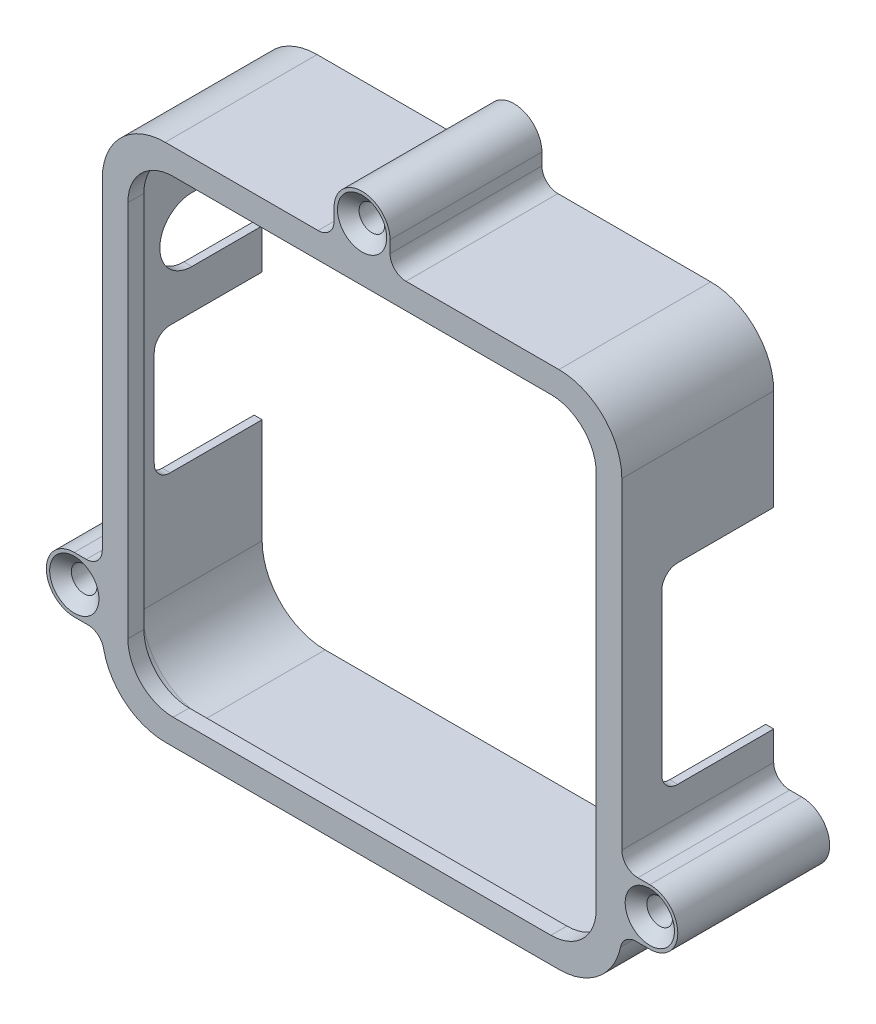
SolidWorks part; units mm, degrees
ref_plane "Front Plane" through (0, 0, 0) normal (0, 0, 1) x (1, 0, 0)
ref_plane "Top Plane" through (0, 0, 0) normal (0, 1, 0) x (1, 0, 0)
ref_plane "Right Plane" through (0, 0, 0) normal (1, 0, 0) x (0, 0, -1)
sketch "Sketch1" plane through (0, 0, 0) normal (0, 0, 1) x (1, 0, 0)
  line L1 (-50, -50) -> (50, -50)
  line L2 (-50, -50) -> (-50, 50)
  line L3 (-50, 50) -> (50, 50)
  line L4 (50, -50) -> (50, 50)
  line L5 (-50, -50) -> (50, 50) construction
  line L6 (-50, 50) -> (50, -50) construction
  line L7 (-51.5875, -51.5875) -> (51.5875, -51.5875)
  line L8 (-51.5875, -51.5875) -> (-51.5875, 51.5875)
  line L9 (-51.5875, 51.5875) -> (51.5875, 51.5875)
  line L10 (51.5875, -51.5875) -> (51.5875, 51.5875)
  line L11 (-51.5875, -51.5875) -> (51.5875, 51.5875) construction
  line L12 (-51.5875, 51.5875) -> (51.5875, -51.5875) construction
  point P0 (0, 0)
  point P6 (0, 0)
  dimension "D1" = 100
  dimension "D2" = 1.5875
extrude "Boss-Extrude1" add sketch "Sketch1" along normal blind 26.9875
fillet "Fillet1" radius 12.5 4 edges at (50, 50, 13.4937) (50, -50, 13.4937) (-50, -50, 13.4937) (-50, 50, 13.4937)
fillet "Fillet2" radius 12.5 4 edges at (51.5875, -51.5875, 13.4937) (51.5875, 51.5875, 13.4937) (-51.5875, -51.5875, 13.4937) (-51.5875, 51.5875, 13.4937)
sketch "Sketch2" plane through (0, 0, 26.9875) normal (0, 0, 1) x (1, 0, 0)
  line L0 (46.5, -37.5) -> (46.5, 37.5)
  line L1 (37.5, 46.5) -> (-37.5, 46.5)
  line L2 (-46.5, 37.5) -> (-46.5, -37.5)
  line L3 (-37.5, -46.5) -> (37.5, -46.5)
  line L4 (-39.0875, -51.5875) -> (39.0875, -51.5875)
  line L5 (51.5875, -39.0875) -> (51.5875, 39.0875)
  line L6 (39.0875, 51.5875) -> (-39.0875, 51.5875)
  line L7 (-51.5875, 39.0875) -> (-51.5875, -39.0875)
  line L8 (-39.0875, -51.5875) -> (39.0875, -51.5875)
  line L9 (51.5875, -39.0875) -> (51.5875, 39.0875)
  line L10 (39.0875, 51.5875) -> (-39.0875, 51.5875)
  line L11 (-51.5875, 39.0875) -> (-51.5875, -39.0875)
  line L12 (50, -37.5) -> (50, 37.5)
  line L13 (-37.5, -50) -> (37.5, -50)
  line L14 (-50, 37.5) -> (-50, -37.5)
  line L15 (37.5, 50) -> (-37.5, 50)
  line L16 (50, -37.5) -> (50, 37.5) construction
  line L17 (-37.5, -50) -> (37.5, -50) construction
  line L18 (-50, 37.5) -> (-50, -37.5) construction
  line L19 (37.5, 50) -> (-37.5, 50) construction
  arc A0 (46.5, 37.5) -> (37.5, 46.5) centre (37.5, 37.5) ccw
  arc A1 (-37.5, 46.5) -> (-46.5, 37.5) centre (-37.5, 37.5) ccw
  arc A2 (-46.5, -37.5) -> (-37.5, -46.5) centre (-37.5, -37.5) ccw
  arc A3 (37.5, -46.5) -> (46.5, -37.5) centre (37.5, -37.5) ccw
  arc A4 (39.0875, -51.5875) -> (51.5875, -39.0875) centre (39.0875, -39.0875) ccw
  arc A5 (51.5875, 39.0875) -> (39.0875, 51.5875) centre (39.0875, 39.0875) ccw
  arc A6 (-39.0875, 51.5875) -> (-51.5875, 39.0875) centre (-39.0875, 39.0875) ccw
  arc A7 (-51.5875, -39.0875) -> (-39.0875, -51.5875) centre (-39.0875, -39.0875) ccw
  arc A8 (39.0875, -51.5875) -> (51.5875, -39.0875) centre (39.0875, -39.0875) ccw
  arc A9 (51.5875, 39.0875) -> (39.0875, 51.5875) centre (39.0875, 39.0875) ccw
  arc A10 (-39.0875, 51.5875) -> (-51.5875, 39.0875) centre (-39.0875, 39.0875) ccw
  arc A11 (-51.5875, -39.0875) -> (-39.0875, -51.5875) centre (-39.0875, -39.0875) ccw
  arc A12 (37.5, -50) -> (50, -37.5) centre (37.5, -37.5) ccw
  arc A13 (-50, -37.5) -> (-37.5, -50) centre (-37.5, -37.5) ccw
  arc A14 (-37.5, 50) -> (-50, 37.5) centre (-37.5, 37.5) ccw
  arc A15 (50, 37.5) -> (37.5, 50) centre (37.5, 37.5) ccw
  arc A16 (37.5, -50) -> (50, -37.5) centre (37.5, -37.5) ccw construction
  arc A17 (-50, -37.5) -> (-37.5, -50) centre (-37.5, -37.5) ccw construction
  arc A18 (-37.5, 50) -> (-50, 37.5) centre (-37.5, 37.5) ccw construction
  arc A19 (50, 37.5) -> (37.5, 50) centre (37.5, 37.5) ccw construction
  dimension "D3" = 93
  dimension "D1" = 0
  dimension "D2" = 0
extrude "Boss-Extrude2" add sketch "Sketch2" along normal blind 3.175
sketch "Sketch3" plane through (-51.5875, 0, 0) normal (-1, 0, 0) x (0, 0, 1)
  line L0 (0, 23.0125) -> (13.97, 23.0125) construction
  line L1 (0, 39.0875) -> (0, -39.0875) construction
  line L2 (0, 29.3625) -> (13.97, 29.3625)
  line L3 (0, 16.6625) -> (13.97, 16.6625)
  line L5 (0, 43.3325) -> (20.32, 43.3325) construction
  line L6 (20.32, 43.3325) -> (20.32, 23.0125) construction
  line L7 (0, 51.5875) -> (30.1625, 51.5875) construction
  arc A0 (0, 29.3625) -> (0, 16.6625) centre (0, 23.0125) ccw
  arc A1 (13.97, 16.6625) -> (13.97, 29.3625) centre (13.97, 23.0125) ccw
  point P4 (6.985, 23.0125)
  dimension "D1" = 22.225
  dimension "D2" = 12.7
  dimension "D3" = 20.32
extrude "Cut-Extrude1" cut sketch "Sketch3" against normal up to next
sketch "Sketch5" plane through (-51.5875, 0, 0) normal (-1, 0, 0) x (0, 0, 1)
  line L0 (15.0812, -39.0875) -> (15.0812, -16.6625) construction
  line L1 (0, -39.0875) -> (30.1625, -39.0875) construction
  line L2 (8.7312, -16.6625) -> (21.4312, -16.6625)
  line L4 (8.7312, 8.7375) -> (21.4312, 8.7375)
  line L5 (21.4312, -16.6625) -> (21.4312, 8.7375)
  line L6 (8.7312, -16.6625) -> (21.4312, 8.7375) construction
  line L7 (8.7312, 8.7375) -> (21.4312, -16.6625) construction
  line L8 (30.1625, -51.5875) -> (0, -51.5875) construction
  line L9 (0, 16.6625) -> (0, -39.0875) construction
  line L10 (8.7312, 8.7375) -> (0, 8.7375)
  line L11 (8.7312, 8.7375) -> (8.7312, -16.6625) construction
  line L12 (8.7312, -16.6625) -> (0, -16.6625)
  line L13 (0, 8.7375) -> (0, -16.6625)
  dimension "D1" = 12.7
  dimension "D2" = 25.4
  dimension "D3" = 34.925
extrude "Cut-Extrude2" cut sketch "Sketch5" against normal up to next
sketch "Sketch6" plane through (51.5875, 0, 0) normal (1, 0, 0) x (0, 0, -1)
  line L0 (0, -39.0875) -> (0, 39.0875) construction
  line L1 (-3.175, -19.05) -> (-22.225, -19.05)
  line L3 (-3.175, 19.05) -> (-22.225, 19.05)
  line L4 (-22.225, -19.05) -> (-22.225, 19.05)
  line L5 (-3.175, -19.05) -> (-22.225, 19.05) construction
  line L6 (-3.175, 19.05) -> (-22.225, -19.05) construction
  line L8 (-3.175, 19.05) -> (0, 19.05)
  line L10 (-3.175, -19.05) -> (0, -19.05)
  line L11 (0, 19.05) -> (0, -19.05)
  point P0 (-12.7, 0)
  dimension "D1" = 38.1
  dimension "D2" = 19.05
  dimension "D3" = 3.175
extrude "Cut-Extrude3" cut sketch "Sketch6" against normal up to next
fillet "Fillet5" radius 3.175 12 edges at (-46.3388, -46.3388, 26.9875) (-50, 0, 26.9875) (-46.3388, 46.3388, 26.9875) (0, 50, 26.9875) (46.3388, 46.3388, 26.9875) (50, 0, 26.9875) (46.3388, -46.3388, 26.9875) (-50.7937, 8.7375, 21.4312) (-50.7937, -16.6625, 21.4312) (0, -50, 26.9875) (50.7937, -19.05, 22.225) (50.7937, 19.05, 22.225)
sketch "Sketch7" plane through (0, 0, 30.1625) normal (0, 0, 1) x (1, 0, 0)
  line L0 (39.0875, 51.5875) -> (-39.0875, 51.5875) construction
  line L1 (57.1437, -27.975) -> (51.5875, -27.975)
  line L2 (57.1437, -27.975) -> (57.1437, -39.0875) construction
  line L3 (57.1437, -39.0875) -> (51.5875, -39.0875)
  line L4 (51.5875, -27.975) -> (51.5875, -39.0875)
  line L5 (-51.5875, -39.0875) -> (-57.1437, -39.0875)
  line L6 (-51.5875, -39.0875) -> (-51.5875, -27.975)
  line L7 (-51.5875, -27.975) -> (-57.1437, -27.975)
  line L8 (-57.1437, -39.0875) -> (-57.1437, -27.975) construction
  line L9 (-5.5562, 51.5875) -> (5.5562, 51.5875)
  line L10 (-5.5562, 51.5875) -> (-5.5562, 57.1437)
  line L11 (-5.5562, 57.1437) -> (5.5563, 57.1437) construction
  line L12 (5.5562, 51.5875) -> (5.5563, 57.1437)
  arc A0 (57.1437, -39.0875) -> (57.1437, -27.975) centre (57.1437, -33.5312) ccw
  arc A1 (-57.1437, -39.0875) -> (-57.1437, -27.975) centre (-57.1437, -33.5313) cw
  arc A2 (5.5563, 57.1437) -> (-5.5562, 57.1437) centre (0, 57.1437) ccw
  point P16 (0, 51.5875)
  dimension "D1" = 5.5562
extrude "Boss-Extrude3" add sketch "Sketch7" against normal up to surface (30.1625 mm away) up to face at (0, 38.6275, 0)
hole_wizard "CSK for #10 Flat Head Machine Screw (100)1" positions "3DSketch1" profile "Sketch8" countersink size "#10" standard "ANSI Inch" end condition up to next
sketch3d "3DSketch1"
  line L0 (57.1437, -33.5312, 0) -> (57.1437, -33.5312, 30.1625) construction
  line L1 (-57.1437, -33.5313, 0) -> (-57.1437, -33.5313, 30.1625) construction
  line L2 (0, 57.1437, 0) -> (0, 57.1437, 30.1625) construction
  point P0 (57.1437, -33.5312, 30.1625)
  point P4 (-57.1437, -33.5313, 30.1625)
  point P8 (0, 57.1437, 30.1625)
sketch "Sketch8" plane through (57.1437, -33.5312, 30.1625) normal (1, 0, 0) x (0, -1, 0)
  line L0 (0, 0) -> (0, 30.1625)
  line L1 (0, 30.1625) -> (2.5527, 30.1625)
  line L2 (2.5527, 30.1625) -> (2.5527, 1.9608)
  line L3 (2.5527, 1.9608) -> (4.8895, 0)
  line L5 (4.8895, 0) -> (0, 0)
  line L6 (-2.5527, 1.9608) -> (-4.8895, 0) construction
  line L11 (0, -6.35) -> (0, 107.95) construction
  dimension "Thru Hole Dia." = 5.1054
  dimension "Thru Hole Depth" = 30.1625
  dimension "Near C'Sink Dia." = 9.779
  dimension "Near C'Sink Angle" = 100
fillet "Fillet4" radius 3.175 6 edges at (-5.5562, 51.5875, 15.0812) (-51.5875, -39.0875, 15.0812) (51.5875, -39.0875, 15.0812) (51.5875, -27.975, 15.0812) (5.5562, 51.5875, 15.0812) (-51.5875, -27.975, 15.0812)
